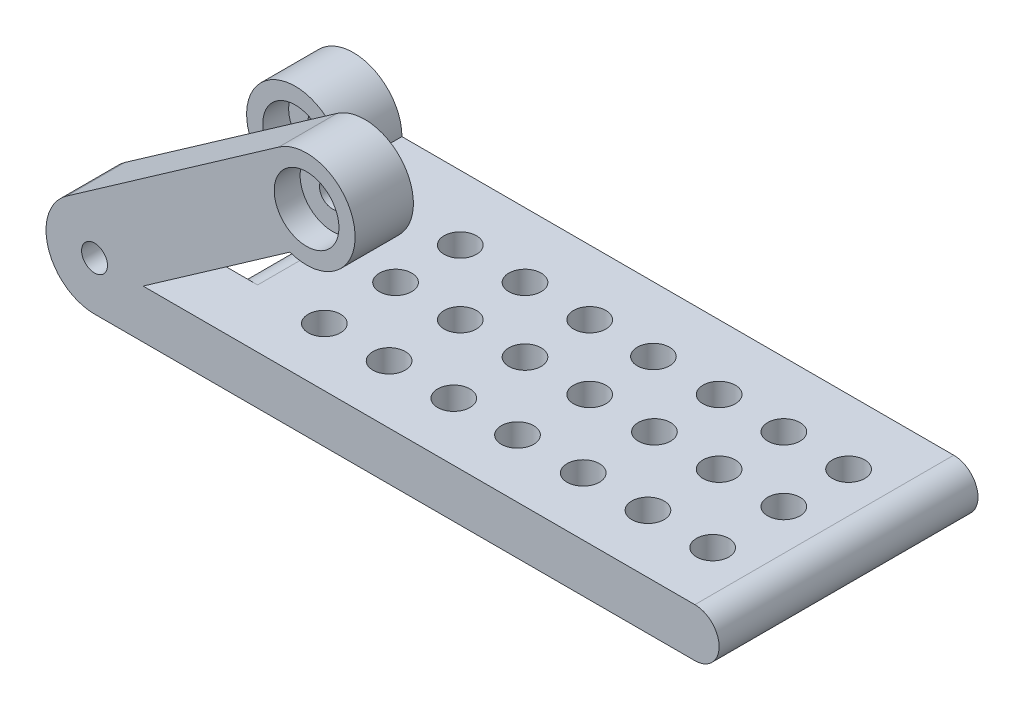
SolidWorks part; units mm, degrees
ref_plane "Front Plane" through (0, 0, 0) normal (0, 0, 1) x (1, 0, 0)
ref_plane "Top Plane" through (0, 0, 0) normal (0, 1, 0) x (1, 0, 0)
ref_plane "Right Plane" through (0, 0, 0) normal (1, 0, 0) x (0, 0, -1)
sketch "Sketch1" plane through (0, 0, 0) normal (0, 0, 1) x (1, 0, 0)
  line L0 (0, 0) -> (123.2164, 0) construction
  line L1 (0, -7.5) -> (92.7661, -7.5)
  line L2 (32.7661, 22.9431) -> (32.7661, 0)
  line L3 (7.5, 0) -> (92.7661, 0)
  line L4 (92.7661, 0) -> (92.7661, -7.5)
  line L5 (0, 0) -> (32.7661, 22.9431)
  line L6 (-4.3018, 6.1436) -> (28.4643, 29.0867)
  line L7 (7.5, 0) -> (30.2009, 15.8954)
  circle A0 centre (0, 0) radius 2
  circle A1 centre (0, 0) radius 7.5
  circle A2 centre (92.7661, -3.75) radius 3.75
  circle A4 centre (32.7661, 22.9431) radius 2
  circle A5 centre (32.7661, 22.9431) radius 7.5
  dimension "D1" = 4
  dimension "D2" = 15
  dimension "D5" = 4
  dimension "D6" = 15
  dimension "D3" = 60
  dimension "D4" = 40
  dimension "D7" = 35
extrude "Boss-Extrude1" add sketch "Sketch1" along normal blind 40 contours A5 L6 A1 L5 | A5 L5 A1 L7 | A5 L5 A4 L2 | L5 A5 L2 A4 | A2 L3 A1 L1 | L4 A2 | L4 A2 | L0 A0 L5 A1 | A0 L0 A1 L5
sketch "Sketch2" plane through (0, -7.5, 0) normal (0, -1, 0) x (1, 0, 0)
  line L0 (0, 0) -> (92.7661, 0) construction
  line L1 (12.5, 31) -> (-7.5, 31)
  line L2 (12.5, 31) -> (12.5, 9)
  line L3 (12.5, 9) -> (-7.5, 9)
  line L4 (-7.5, 31) -> (-7.5, 9)
  line L5 (12.5, 31) -> (-7.5, 9) construction
  line L6 (12.5, 9) -> (-7.5, 31) construction
  line L7 (-7.5, 40) -> (-7.5, 0) construction
  point P0 (2.5, 20)
  dimension "D1" = 22
  dimension "D2" = 9
  dimension "D3" = 20
extrude "Cut-Extrude1" cut sketch "Sketch2" against normal through all
sketch "Sketch3" plane through (0, 0, 0) normal (0, 0, -1) x (-1, 0, 0)
  line L0 (-7.5, 0) -> (-30.2009, 15.8954)
  line L1 (-30.2009, 15.8954) -> (-35.9092, 12.7716)
  line L2 (-35.9092, 12.7716) -> (-48.7321, 24.7575)
  line L3 (-48.7321, 24.7575) -> (-40.6828, 33.3689)
  line L4 (-40.6828, 33.3689) -> (-18.8505, 32.1055)
  line L5 (-18.8505, 32.1055) -> (5.4663, 20.3721)
  line L6 (5.4663, 20.3721) -> (4.3018, 6.1436)
  line L7 (4.3018, 6.1436) -> (-7.5, 0)
  circle A0 centre (0, 0) radius 7.5
  circle M1 centre (-32.7661, 22.9431) radius 2
  line M2 (-30.2009, 15.8954) -> (-7.5, 0)
  line M7 (4.3018, 6.1436) -> (-28.4643, 29.0867)
  arc M8 (-28.4643, 29.0867) -> (-30.2009, 15.8954) centre (-32.7661, 22.9431) ccw
extrude "Cut-Extrude2" cut sketch "Sketch3" against normal blind 31 contours A0 M7 M8 M2 M1
fillet "Fillet1" radius 3.7 2 edges at (12.5, -7.5, 20) (12.5, 0, 20)
sketch "Sketch4" plane through (0, 0, 0) normal (0, 1, 0) x (1, 0, 0)
  line L0 (16.2, -10) -> (96.5161, -10) construction
  line L1 (16.2, -9) -> (16.2, -31) construction
  line L2 (96.5161, -40) -> (96.5161, 0) construction
  line L3 (16.2, -20) -> (96.5161, -20) construction
  line L4 (16.2, -31) -> (96.5161, -31) construction
  line L5 (36.5161, 0) -> (36.5161, -40) construction
  line L6 (7.5, 0) -> (92.7661, 0) construction
  line L7 (7.5, -40) -> (92.7661, -40) construction
  line L8 (46.5161, 0) -> (46.5161, -40) construction
  line L9 (56.5161, 0) -> (56.5161, -40) construction
  line L10 (66.5161, 0) -> (66.5161, -40) construction
  line L11 (76.5161, -40) -> (76.5161, 0) construction
  line L12 (86.5161, 0) -> (86.5161, -40) construction
  line L13 (26.5161, 0) -> (26.5161, -40) construction
  circle A0 centre (86.5161, -10) radius 2.5
  circle A1 centre (86.5161, -20) radius 2.5
  circle A2 centre (86.5161, -31) radius 2.5
  circle A3 centre (76.5161, -31) radius 2.5
  circle A4 centre (76.5161, -20) radius 2.5
  circle A5 centre (76.5161, -10) radius 2.5
  circle A6 centre (66.5161, -10) radius 2.5
  circle A7 centre (66.5161, -20) radius 2.5
  circle A8 centre (66.5161, -31) radius 2.5
  circle A9 centre (56.358, -31) radius 2.5
  circle A10 centre (56.5161, -20) radius 2.5
  circle A11 centre (56.358, -10) radius 2.5
  circle A12 centre (46.5161, -10) radius 2.5
  circle A13 centre (46.5161, -20) radius 2.5
  circle A14 centre (46.5161, -31) radius 2.5
  circle A15 centre (36.5161, -31) radius 2.5
  circle A16 centre (36.5161, -20) radius 2.5
  circle A17 centre (36.5161, -10) radius 2.5
  circle A18 centre (26.5161, -10) radius 2.5
  circle A19 centre (26.5161, -20) radius 2.5
  circle A20 centre (26.5161, -31) radius 2.5
  dimension "D8" = 5
  dimension "D1" = 10
  dimension "D2" = 10
  dimension "D3" = 10
  dimension "D4" = 10
  dimension "D5" = 10
  dimension "D6" = 10
  dimension "D7" = 10
extrude "Cut-Extrude3" cut sketch "Sketch4" against normal blind 30
sketch "Sketch5" plane through (0, 0, 9) normal (0, 0, 1) x (1, 0, 0)
  circle A0 centre (0, 0) radius 5
  dimension "D1" = 10
extrude "Cut-Extrude4" cut sketch "Sketch5" against normal blind 4
sketch "Sketch11" plane through (0, 0, 31) normal (0, 0, -1) x (-1, 0, 0)
  circle A0 centre (0, 0) radius 5
  dimension "D1" = 10
extrude "Cut-Extrude6" cut sketch "Sketch11" against normal blind 4
sketch "Sketch12" plane through (0, 0, 40) normal (0, 0, 1) x (1, 0, 0)
  circle A0 centre (32.7661, 22.9431) radius 5
  dimension "D1" = 10
extrude "Cut-Extrude7" cut sketch "Sketch12" against normal blind 4
